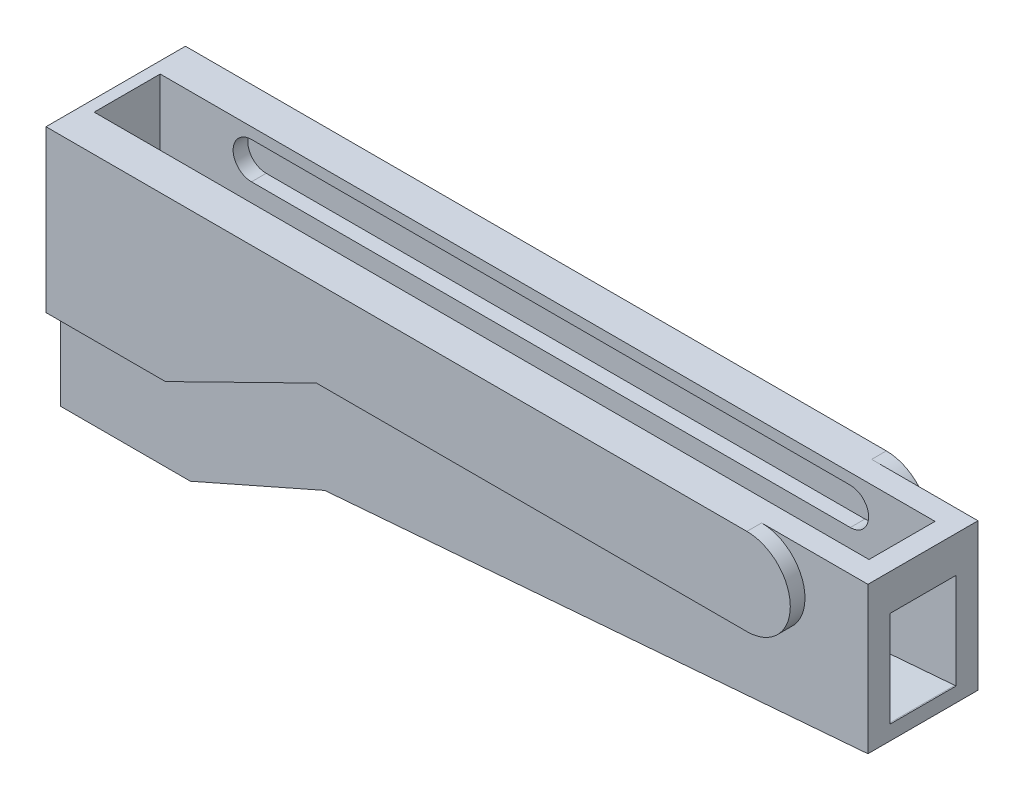
SolidWorks part; units mm, degrees
ref_plane "Front Plane" through (0, 0, 0) normal (0, 0, 1) x (1, 0, 0)
ref_plane "Top Plane" through (0, 0, 0) normal (0, 1, 0) x (1, 0, 0)
ref_plane "Right Plane" through (0, 0, 0) normal (1, 0, 0) x (0, 0, -1)
sketch "Sketch1" plane through (0, 0, 0) normal (0, 0, 1) x (1, 0, 0)
  line L0 (27.5, 8.5) -> (27.5, -1.5)
  line L1 (-27.5, -8.5) -> (-18.6638, -8.5)
  line L2 (-27.5, -8.5) -> (-27.5, 8.5)
  line L3 (-27.5, 8.5) -> (27.5, 8.5)
  line L4 (27.5, -1.5) -> (27.5, 8.5)
  line L5 (-27.5, -8.5) -> (27.5, 8.5) construction
  line L6 (-27.5, 8.5) -> (9.5164, -2.9414) construction
  line L7 (27.5, -1.5) -> (-9.5133, -4.4667)
  line L8 (-9.5133, -4.4667) -> (-18.6638, -8.5)
  point P0 (0, 0)
  dimension "D1" = 55
  dimension "D3" = 10
  dimension "D4" = 4.583
  dimension "D5" = 23.786
  dimension "D6" = 10
extrude "Boss-Extrude1" add sketch "Sketch1" along normal blind 1.5 from offset 3 contours L8 L7 L0 L3 L2 L1
sketch "Sketch2" plane through (0, 0, 4.5) normal (0, 0, 1) x (1, 0, 0)
  line L0 (-27.5, -2.4687) -> (-19.3628, -2.4687)
  line L1 (-27.5, -8.5) -> (-27.5, 8.5) construction
  line L2 (-19.3628, -2.4687) -> (-9.0717, 2.5877)
  line L3 (-9.0717, 2.5877) -> (20.2551, 2.5877)
  line L4 (-27.5, 8.5) -> (27.5, 8.5) construction
  line L5 (-27.5, -2.4687) -> (-27.5, 8.5)
  line L6 (-27.5, 8.5) -> (20.2551, 8.5)
  arc A0 (20.2551, 8.5) -> (20.2551, 2.5877) centre (20.2551, 5.5438) cw
extrude "Boss-Extrude2" add sketch "Sketch2" along normal blind 1
sketch "Sketch3" plane through (0, 0, 3) normal (0, 0, -1) x (-1, 0, 0)
  line L0 (27.5, 8.5) -> (-27.5, 8.5) construction
  line L1 (-20.2968, 7.75) -> (20.5, 7.75)
  line L3 (-20.2968, 5.25) -> (20.5, 5.25)
  line L5 (-27.5, 8.5) -> (-27.5, -1.5) construction
  line L6 (27.5, -8.5) -> (27.5, 8.5) construction
  arc A0 (-20.2968, 7.75) -> (-20.2968, 5.25) centre (-20.2968, 6.5) ccw
  arc A1 (20.5, 7.75) -> (20.5, 5.25) centre (20.5, 6.5) cw
  dimension "D1" = 2.5
  dimension "D2" = 2
  dimension "D3" = 7
  dimension "D4" = 7.2032
extrude "Cut-Extrude1" cut sketch "Sketch3" against normal blind 1.5
sketch "Sketch5" plane through (0, 0, 0) normal (0, 0, 1) x (1, 0, 0)
  line L0 (27.5, -1.5) -> (-9.5133, -4.4667)
  line L1 (27.5, 8.5) -> (-27.5, 8.5)
  line L2 (27.5, 8.5) -> (27.5, -1.5)
  line L3 (-18.6638, -8.5) -> (-27.5, -8.5)
  line L4 (-27.5, 8.5) -> (-27.5, -8.5)
  line L5 (-9.5133, -4.4667) -> (-18.6638, -8.5)
extrude "Boss-Extrude3" add sketch "Sketch5" along normal blind 1.5 from offset 3 separate body offset against normal yes
sketch "Sketch7" plane through (0, 0, -3) normal (0, 0, -1) x (-1, 0, 0)
  line L6 (-20.2551, 8.5) -> (27.5, 8.5)
  line L7 (9.0717, 2.5877) -> (-20.2551, 2.5877)
  line L8 (19.3628, -2.4687) -> (9.0717, 2.5877)
  line L9 (27.5, -2.4687) -> (19.3628, -2.4687)
  line L10 (27.5, 8.5) -> (27.5, -2.4687)
  arc A1 (-20.2551, 2.5877) -> (-20.2551, 8.5) centre (-20.2551, 5.5438) cw
  point P0 (27.5, 8.5)
extrude "Boss-Extrude4" add sketch "Sketch7" along normal blind 1
sketch "Sketch8" plane through (0, 0, 3) normal (0, 0, -1) x (-1, 0, 0)
  line L0 (-27.5, -1.5) -> (9.5133, -4.4667)
  line L1 (18.6638, -8.5) -> (9.5133, -4.4667) construction
  line L2 (9.5133, -4.4667) -> (-27.5, -1.5) construction
  line L3 (9.5133, -4.4667) -> (18.6638, -8.5)
  line L4 (18.6638, -8.5) -> (27.5, -8.5)
  line L5 (27.5, -8.5) -> (27.5, -7.5)
  line L6 (27.5, -2.4687) -> (27.5, -8.5) construction
  line L7 (-27.4201, -0.5032) -> (9.7618, -3.4834)
  line L8 (9.7618, -3.4834) -> (18.8744, -7.5)
  line L9 (18.8744, -7.5) -> (26.5, -7.5)
  line L10 (26.5, -7.5) -> (26.5, -7.5)
  line L11 (26.5, -7.5) -> (27.5, -7.5)
  line L12 (-27.4201, -0.5032) -> (-27.5, -0.5032)
  line L13 (-27.5, -1.5) -> (-27.5, 8.5) construction
  line L14 (-27.5, -0.5032) -> (-27.5, -1.5)
  line M9 (9.5133, -4.4667) -> (18.6638, -8.5)
  line M10 (18.6638, -8.5) -> (27.5, -8.5)
  line M11 (27.5, -8.5) -> (27.5, 8.5)
  line M13 (-27.5, 8.5) -> (-27.5, -1.5)
  line M14 (-27.5, -1.5) -> (9.5133, -4.4667)
  dimension "D1" = 1
  dimension "D2" = 1
extrude "Boss-Extrude5" add sketch "Sketch8" along normal up to surface (4.5 mm away) contours L7 L12 L11 L9 L8 M13 M14 M9 M10 M11 up to face at (-4.6962, -0.9945, -1.5)
sketch "Sketch9" plane through (0, 0, -1.5) normal (0, 0, 1) x (1, 0, 0)
  line L0 (-20.5, 7.75) -> (20.2968, 7.75)
  line L1 (-20.5, 5.25) -> (20.2968, 5.25)
  line L2 (-27.5, 8.5) -> (-27.5, -7.5) construction
  line L3 (27.5, 8.5) -> (-27.5, 8.5) construction
  line L4 (27.5, -0.5032) -> (27.5, 8.5) construction
  arc A0 (-20.5, 7.75) -> (-20.5, 5.25) centre (-20.5, 6.5) ccw
  arc A1 (20.2968, 7.75) -> (20.2968, 5.25) centre (20.2968, 6.5) cw
  dimension "D1" = 7
  dimension "D2" = 2
  dimension "D3" = 7.2032
extrude "Cut-Extrude2" cut sketch "Sketch9" against normal blind 1
sketch "Sketch10" plane through (0, 0, 3) normal (0, 0, -1) x (-1, 0, 0)
  line L5 (27.5, 8.5) -> (26.7198, 8.5)
  line L6 (27.5, 8.5) -> (27.5, 3.5137)
  line L7 (27.5, 3.5137) -> (26.7198, 3.5137)
  line L8 (26.7198, 8.5) -> (26.7198, 3.5137)
extrude "Boss-Extrude6" add sketch "Sketch10" along normal up to surface (4.5 mm away) up to face at (-0.1016, 6.5, -1.5)
sketch "Sketch11" plane through (0, 0, -1.5) normal (0, 0, 1) x (1, 0, 0)
  line L1 (27.5, 8.5) -> (26.0733, 8.5)
  line L2 (27.5, 8.5) -> (27.5, 6.0285)
  line L3 (27.5, 6.0285) -> (26.0733, 6.0285)
  line L4 (26.0733, 8.5) -> (26.0733, 6.0285)
extrude "Boss-Extrude7" add sketch "Sketch11" along normal up to surface (4.5 mm away) up to face at (-0.1016, 6.5, 3)
sketch "Sketch12" plane through (0, 0, -1.5) normal (0, 0, 1) x (1, 0, 0)
  point P0 (20.2968, 6.5)
  point P1 (20.2968, 0)
  dimension "D1" = 6.5
